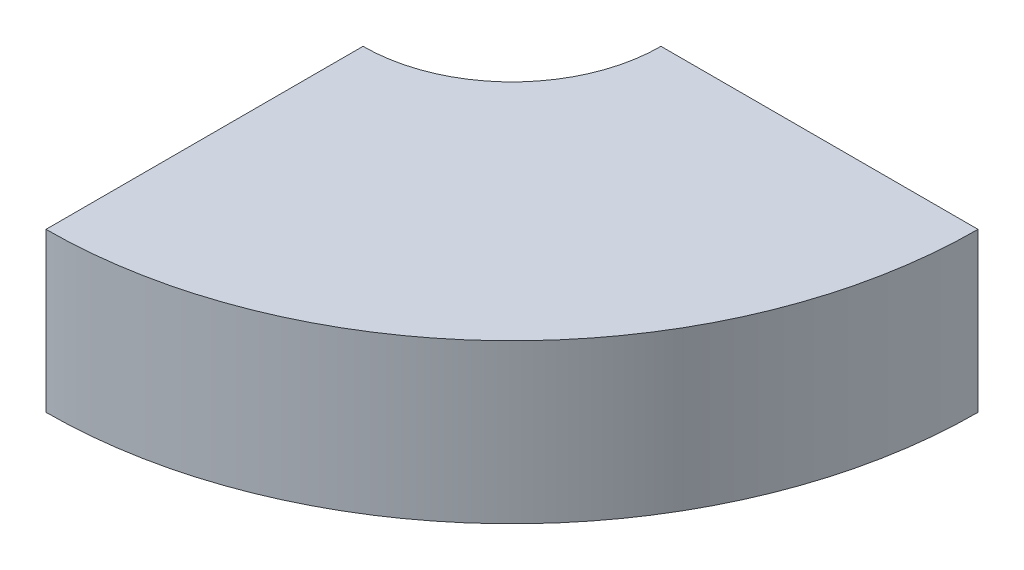
SolidWorks part; units mm, degrees
ref_plane "Front Plane" through (0, 0, 0) normal (0, 0, 1) x (1, 0, 0)
ref_plane "Top Plane" through (0, 0, 0) normal (0, 1, 0) x (1, 0, 0)
ref_plane "Right Plane" through (0, 0, 0) normal (1, 0, 0) x (0, 0, -1)
sketch "Sketch2" plane through (0, 0, 0) normal (0, 1, 0) x (1, 0, 0)
  line L0 (1.88, 0) -> (5.88, 0)
  line L1 (0, -1.88) -> (0, -5.88)
  arc A2 (0, -5.88) -> (5.88, 0) centre (0, 0) ccw
  arc A3 (0, -1.88) -> (1.88, 0) centre (0, 0) ccw
  dimension "D3" = 90
  dimension "D1" = 4
  dimension "D2" = 1.88
  dimension "D5" = 1.88
extrude "Boss-Extrude1" add sketch "Sketch2" along normal blind 2
